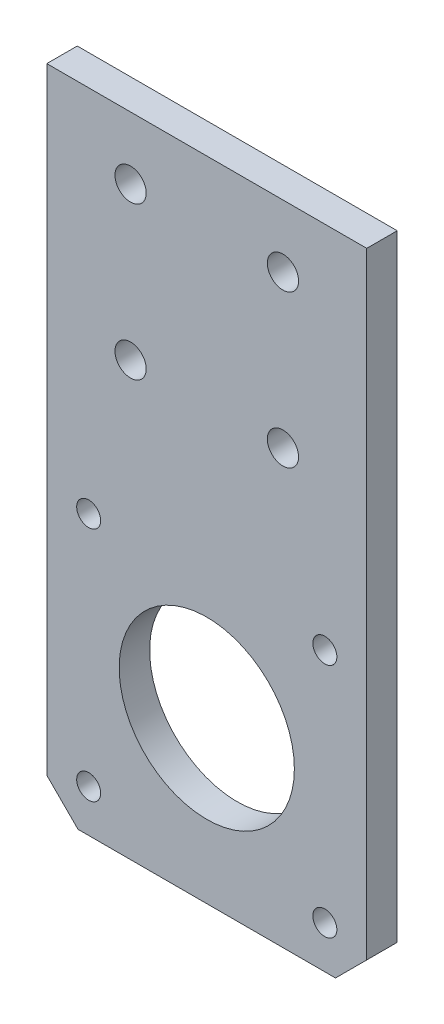
SolidWorks part; units mm, degrees
ref_plane "Alzado" through (0, 0, 0) normal (0, 0, 1) x (1, 0, 0)
ref_plane "Planta" through (0, 0, 0) normal (0, 1, 0) x (1, 0, 0)
ref_plane "Vista lateral" through (0, 0, 0) normal (1, 0, 0) x (0, 0, -1)
sketch "Croquis1" plane through (0, 0, 0) normal (0, 0, 1) x (1, 0, 0)
  line L0 (11, 56.8) -> (31, 76.8) construction
  line L1 (0, 85) -> (42, 85)
  line L2 (0, 85) -> (0, 0)
  line L3 (0, 0) -> (42, 0)
  line L4 (42, 85) -> (42, 0)
  line L5 (21, 66.8) -> (21, 85) construction
  circle A0 centre (11, 76.8) radius 2.05
  circle A1 centre (31, 76.8) radius 2.05
  circle A4 centre (31, 56.8) radius 2.05
  circle A5 centre (11, 56.8) radius 2.05
  circle A6 centre (21, 21.08) radius 2.55
  dimension "D3" = 4.1
  dimension "D11" = 5.1
  dimension "D1" = 42
  dimension "D2" = 85
  dimension "D4" = 20
  dimension "D5" = 63.92
  dimension "D6" = 8.2
  dimension "D7" = 20
extrude "Saliente-Extruir1" add sketch "Croquis1" along normal blind 4
sketch "Croquis5" plane through (0, 0, 4) normal (0, 0, 1) x (1, 0, 0)
  line L0 (5.5, 36.58) -> (36.5, 5.58) construction
  line L2 (36.5, 36.58) -> (5.5, 5.58) construction
  circle A0 centre (21, 21.08) radius 11.5
  circle A1 centre (5.5, 36.58) radius 1.575
  circle A2 centre (36.5, 36.58) radius 1.575
  circle A3 centre (36.5, 5.58) radius 1.575
  circle A4 centre (5.5, 5.58) radius 1.575
  dimension "D1" = 23
  dimension "D4" = 3.15
  dimension "D2" = 31
  dimension "D3" = 31
extrude "Cortar-Extruir2" cut sketch "Croquis5" against normal through all
chamfer "Chaflán1" distance 4.1 angle 45 2 edges at (42, 0, 2) (0, 0, 2)
